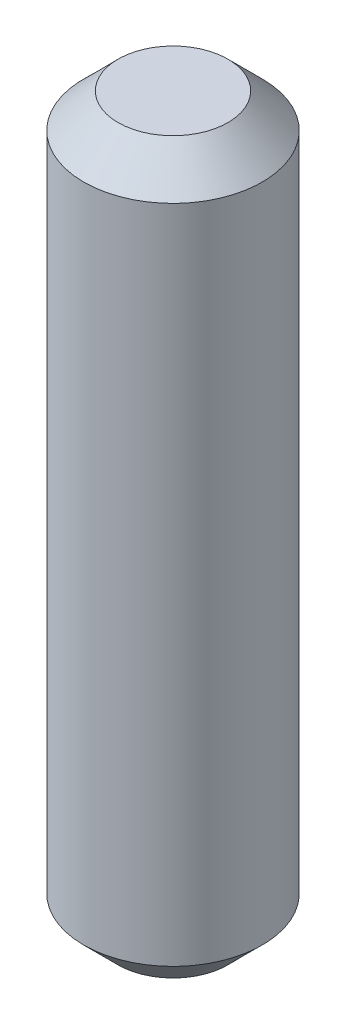
SolidWorks part; units mm, degrees
ref_plane "Front Plane" through (0, 0, 0) normal (0, 0, 1) x (1, 0, 0)
ref_plane "Top Plane" through (0, 0, 0) normal (0, 1, 0) x (1, 0, 0)
ref_plane "Right Plane" through (0, 0, 0) normal (1, 0, 0) x (0, 0, -1)
sketch "Sketch2" plane through (0, 0, 0) normal (0, 1, 0) x (1, 0, 0)
  circle A0 centre (0, 0) radius 1.651
  dimension "D1" = 3.302
extrude "Boss-Extrude1" add sketch "Sketch2" along normal blind 13.4874
chamfer "Chamfer1" distance 0.635 angle 45 2 edges at (0, 0, 1.651) (0, 13.4874, 1.651)
